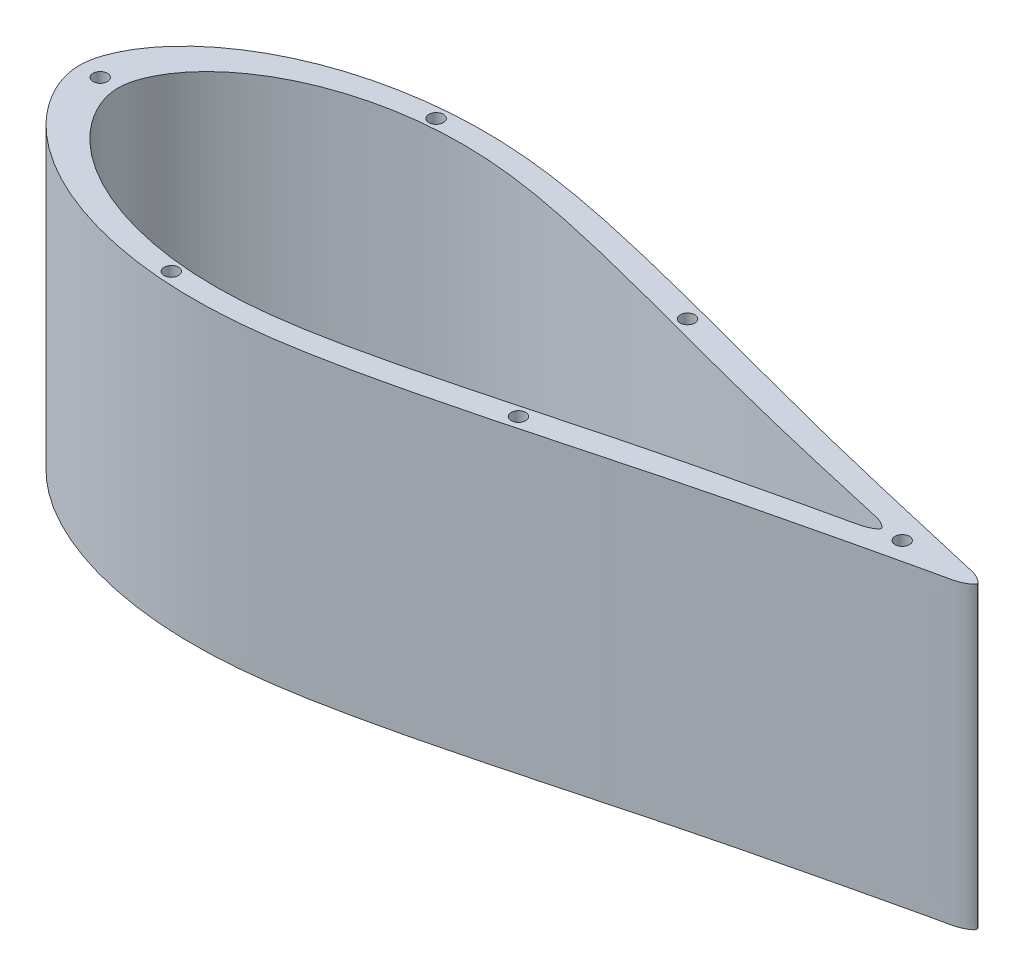
SolidWorks part; units mm, degrees
material "6061 Alloy"
ref_plane "Front Plane" through (0, 0, 0) normal (0, 0, 1) x (1, 0, 0)
ref_plane "Top Plane" through (0, 0, 0) normal (0, 1, 0) x (1, 0, 0)
ref_plane "Right Plane" through (0, 0, 0) normal (1, 0, 0) x (0, 0, -1)
curve "Curve2"
  spline degree 3 poles (0.6483, 0, -5.7987) (-0.3085, 0, 0) (0.6483, 0, 5.7987) (3.0311, 0, 11.5336) (6.6533, 0, 17.267) (11.4717, 0, 22.8371) (17.4302, 0, 28.1154) (24.4659, 0, 32.9986) (32.5279, 0, 37.3723) (41.5389, 0, 41.1607) (51.4314, 0, 44.2651) (62.1158, 0, 46.6282) (73.526, 0, 48.1549) (85.6114, 0, 48.7284) (98.3426, 0, 48.3105) (111.7257, 0, 46.8479) (125.7606, 0, 44.4122) (140.4343, 0, 41.2887) (155.6347, 0, 37.6615) (171.177, 0, 33.6995) (186.8539, 0, 29.5664) (202.4318, 0, 25.4194) (217.9957, 0, 21.2663) (233.2084, 0, 17.405) (247.6838, 0, 13.8748) (260.7251, 0, 10.7897) (272.1052, 0, 8.143) (281.7116, 0, 5.9794) (289.2075, 0, 4.169) (295.0367, 0, 3.0969) (298.1709, 0, 1.895) (300.5776, 0, 0) (298.1709, 0, -1.895) (295.0367, 0, -3.0969) (289.2075, 0, -4.169) (281.7116, 0, -5.9794) (272.1052, 0, -8.143) (260.7251, 0, -10.7897) (247.6838, 0, -13.8748) (233.2084, 0, -17.405) (217.9957, 0, -21.2663) (202.4318, 0, -25.4194) (186.8539, 0, -29.5664) (171.177, 0, -33.6995) (155.6347, 0, -37.6615) (140.4343, 0, -41.2887) (125.7606, 0, -44.4122) (111.7257, 0, -46.8479) (98.3426, 0, -48.3105) (85.6114, 0, -48.7284) (73.526, 0, -48.1549) (62.1158, 0, -46.6282) (51.4314, 0, -44.2651) (41.5389, 0, -41.1607) (32.5279, 0, -37.3723) (24.4659, 0, -32.9986) (17.4302, 0, -28.1154) (11.4717, 0, -22.8371) (6.6533, 0, -17.267) (3.0311, 0, -11.5336) (0.6483, 0, -5.7987) (-0.3085, 0, 0) (0.6483, 0, 5.7987) knots -0.028335 -0.018012 -0.008569 0 0.008569 0.018012 0.028335 0.039554 0.051691 0.064762 0.078763 0.093696 0.109541 0.126268 0.143841 0.162293 0.181715 0.202223 0.224008 0.247042 0.271046 0.295702 0.320629 0.34543 0.369662 0.394535 0.417436 0.438027 0.456004 0.47109 0.483065 0.49175 0.497395 0.5 0.502605 0.50825 0.516935 0.52891 0.543996 0.561973 0.582564 0.605465 0.630338 0.65457 0.679371 0.704298 0.728954 0.752958 0.775992 0.797777 0.818285 0.837707 0.856159 0.873732 0.890459 0.906304 0.921237 0.935238 0.948309 0.960446 0.971665 0.981988 0.991431 1 1.008569 1.018012 1.028335 periodic
sketch "Sketch3" plane through (0, 0, 0) normal (0, 1, 0) x (1, 0, 0)
  spline S0 degree 3 poles (0.6483, 5.7987) (-0.3085, 0) (0.6483, -5.7987) (3.0311, -11.5336) (6.6533, -17.267) (11.4717, -22.8371) (17.4302, -28.1154) (24.4659, -32.9986) (32.5279, -37.3723) (41.5389, -41.1607) (51.4314, -44.2651) (62.1158, -46.6282) (73.526, -48.1549) (85.6114, -48.7284) (98.3426, -48.3105) (111.7257, -46.8479) (125.7606, -44.4122) (140.4343, -41.2887) (155.6347, -37.6615) (171.177, -33.6995) (186.8539, -29.5664) (202.4318, -25.4194) (217.9957, -21.2663) (233.2084, -17.405) (247.6838, -13.8748) (260.7251, -10.7897) (272.1052, -8.143) (281.7116, -5.9794) (289.2075, -4.169) (295.0367, -3.0969) (298.1709, -1.895) (300.5776, 0) (298.1709, 1.895) (295.0367, 3.0969) (289.2075, 4.169) (281.7116, 5.9794) (272.1052, 8.143) (260.7251, 10.7897) (247.6838, 13.8748) (233.2084, 17.405) (217.9957, 21.2663) (202.4318, 25.4194) (186.8539, 29.5664) (171.177, 33.6995) (155.6347, 37.6615) (140.4343, 41.2887) (125.7606, 44.4122) (111.7257, 46.8479) (98.3426, 48.3105) (85.6114, 48.7284) (73.526, 48.1549) (62.1158, 46.6282) (51.4314, 44.2651) (41.5389, 41.1607) (32.5279, 37.3723) (24.4659, 32.9986) (17.4302, 28.1154) (11.4717, 22.8371) (6.6533, 17.267) (3.0311, 11.5336) (0.6483, 5.7987) (-0.3085, 0) (0.6483, -5.7987) knots -0.028335 -0.018012 -0.008569 0 0.008569 0.018012 0.028335 0.039554 0.051691 0.064762 0.078763 0.093696 0.109541 0.126268 0.143841 0.162293 0.181715 0.202223 0.224008 0.247042 0.271046 0.295702 0.320629 0.34543 0.369662 0.394535 0.417436 0.438027 0.456004 0.47109 0.483065 0.49175 0.497395 0.5 0.502605 0.50825 0.516935 0.52891 0.543996 0.561973 0.582564 0.605465 0.630338 0.65457 0.679371 0.704298 0.728954 0.752958 0.775992 0.797777 0.818285 0.837707 0.856159 0.873732 0.890459 0.906304 0.921237 0.935238 0.948309 0.960446 0.971665 0.981988 0.991431 1 1.008569 1.018012 1.028335 only from (0, 0) to (0, 0) construction
  spline S1 degree 3 poles (0.6483, 5.7987) (-0.3085, 0) (0.6483, -5.7987) (3.0311, -11.5336) (6.6533, -17.267) (11.4717, -22.8371) (17.4302, -28.1154) (24.4659, -32.9986) (32.5279, -37.3723) (41.5389, -41.1607) (51.4314, -44.2651) (62.1158, -46.6282) (73.526, -48.1549) (85.6114, -48.7284) (98.3426, -48.3105) (111.7257, -46.8479) (125.7606, -44.4122) (140.4343, -41.2887) (155.6347, -37.6615) (171.177, -33.6995) (186.8539, -29.5664) (202.4318, -25.4194) (217.9957, -21.2663) (233.2084, -17.405) (247.6838, -13.8748) (260.7251, -10.7897) (272.1052, -8.143) (281.7116, -5.9794) (289.2075, -4.169) (295.0367, -3.0969) (298.1709, -1.895) (300.5776, 0) (298.1709, 1.895) (295.0367, 3.0969) (289.2075, 4.169) (281.7116, 5.9794) (272.1052, 8.143) (260.7251, 10.7897) (247.6838, 13.8748) (233.2084, 17.405) (217.9957, 21.2663) (202.4318, 25.4194) (186.8539, 29.5664) (171.177, 33.6995) (155.6347, 37.6615) (140.4343, 41.2887) (125.7606, 44.4122) (111.7257, 46.8479) (98.3426, 48.3105) (85.6114, 48.7284) (73.526, 48.1549) (62.1158, 46.6282) (51.4314, 44.2651) (41.5389, 41.1607) (32.5279, 37.3723) (24.4659, 32.9986) (17.4302, 28.1154) (11.4717, 22.8371) (6.6533, 17.267) (3.0311, 11.5336) (0.6483, 5.7987) (-0.3085, 0) (0.6483, -5.7987) knots -0.028335 -0.018012 -0.008569 0 0.008569 0.018012 0.028335 0.039554 0.051691 0.064762 0.078763 0.093696 0.109541 0.126268 0.143841 0.162293 0.181715 0.202223 0.224008 0.247042 0.271046 0.295702 0.320629 0.34543 0.369662 0.394535 0.417436 0.438027 0.456004 0.47109 0.483065 0.49175 0.497395 0.5 0.502605 0.50825 0.516935 0.52891 0.543996 0.561973 0.582564 0.605465 0.630338 0.65457 0.679371 0.704298 0.728954 0.752958 0.775992 0.797777 0.818285 0.837707 0.856159 0.873732 0.890459 0.906304 0.921237 0.935238 0.948309 0.960446 0.971665 0.981988 0.991431 1 1.008569 1.018012 1.028335 only from (0, 0) to (0, 0)
extrude "Boss-Extrude1" add sketch "Sketch3" along normal blind 100
sketch "Sketch4" plane through (0, 0, 0) normal (0, -1, 0) x (1, 0, 0)
  spline S1 degree 3 poles (299.9957, 0.014) (299.9938, -0.0895) (299.9638, -0.2086) (299.9031, -0.3373) (299.8291, -0.4596) (299.7174, -0.5996) (299.5918, -0.7263) (299.4861, -0.8218) (299.4046, -0.8909) (299.3213, -0.9578) (299.2087, -1.0447) (299.0654, -1.1499) (298.8903, -1.2715) (298.7126, -1.3891) (298.3525, -1.6168) (297.92, -1.8622) (297.411, -2.1134) (297.0223, -2.287) (296.6272, -2.4451) (296.2267, -2.5893) (295.822, -2.722) (295.4141, -2.8452) (295.0041, -2.961) (294.5925, -3.0704) (294.0419, -3.2092) (293.4889, -3.3386) (292.9344, -3.4614) (292.5179, -3.5509) (292.101, -3.6386) (291.5448, -3.754) (290.9884, -3.8677) (290.4319, -3.9815) (289.8757, -4.0959) (289.1809, -4.2414) (288.3483, -4.4216) (286.6852, -4.7905) (284.1958, -5.3676) (281.4314, -6.0157) (279.2189, -6.5298) (277.0055, -7.0405) (274.7915, -7.5479) (272.5773, -8.0547) (270.9166, -8.4349) (269.2562, -8.816) (267.0427, -9.3258) (264.2767, -9.9669) (259.8527, -10.9999) (254.3255, -12.3029) (248.8019, -13.6215) (244.3858, -14.6874) (239.9714, -15.7609) (234.4573, -17.1179) (228.9488, -18.4974) (224.5457, -19.6156) (217.945, -21.3082) (208.0596, -23.9078) (194.8919, -27.424) (183.9159, -30.3428) (175.1284, -32.6526) (166.3345, -34.9377) (158.628, -36.8918) (152.0088, -38.511) (148.6961, -39.3081) (145.3801, -40.0913) (142.0605, -40.8591) (138.737, -41.6097) (135.4091, -42.3409) (132.0764, -43.0503) (127.626, -43.9641) (122.0492, -45.0405) (113.0926, -46.5738) (104.0773, -47.7374) (95.0123, -48.3913) (88.1991, -48.6052) (81.3834, -48.5233) (74.5794, -48.1282) (67.8019, -47.4032) (61.0693, -46.3378) (54.4011, -44.9234) (47.8168, -43.1503) (41.3469, -40.998) (35.028, -38.4414) (28.8957, -35.456) (23.013, -32.0075) (18.3744, -28.7213) (14.8691, -25.8285) (12.3582, -23.5227) (9.984, -21.0765) (8.1373, -18.9185) (6.7509, -17.1189) (5.7603, -15.7327) (4.8235, -14.3098) (3.9449, -12.8503) (3.2654, -11.6036) (2.7565, -10.5882) (2.0291, -9.0471) (1.0809, -6.6677) (0.2183, -3.3645) (-0.1054, 0.0396) (0.2336, 3.4379) (0.961, 6.1924) (1.7397, 8.3272) (2.4132, 9.8934) (3.1645, 11.4234) (3.9845, 12.9173) (4.8661, 14.375) (6.1184, 16.2702) (8.4977, 19.4595) (11.5773, 22.8096) (14.9283, 25.8792) (17.5601, 28.0457) (20.2943, 30.0805) (22.6482, 31.6695) (24.5714, 32.8789) (26.5195, 34.0477) (29.9892, 35.9887) (35.0983, 38.4733) (41.419, 41.0252) (46.8122, 42.8146) (51.1842, 44.0565) (55.5891, 45.1756) (63.3708, 46.8228) (74.6452, 48.3036) (88.2816, 48.7503) (101.9024, 48.0274) (113.1705, 46.5598) (122.1264, 45.0264) (128.8176, 43.735) (135.487, 42.3362) (142.1376, 40.8488) (148.7724, 39.2926) (157.6025, 37.1514) (173.0143, 33.2397) (190.5764, 28.5711) (208.1372, 23.899) (221.3117, 20.4089) (234.5313, 17.0929) (245.5623, 14.3906) (254.4011, 12.2854) (261.0337, 10.722) (266.5649, 9.436) (270.9921, 8.4173) (274.3131, 7.6559) (277.6343, 6.8948) (280.9537, 6.1266) (284.2713, 5.3501) (287.59, 4.5785) (290.368, 3.9915) (292.5952, 3.5417) (294.2576, 3.1677) (295.6314, 2.798) (296.7027, 2.4227) (297.4846, 2.0873) (298.1125, 1.7565) (298.5991, 1.4632) (298.8968, 1.2692) (299.1297, 1.1058) (299.3003, 0.9778) (299.438, 0.8649) (299.5442, 0.7698) (299.6215, 0.6957) (299.6958, 0.6184) (299.7894, 0.5104) (299.8729, 0.3935) (299.9377, 0.2672) (299.9677, 0.1847) (299.984, 0.117) (299.9921, 0.0657) (299.9957, 0.014) (299.9938, -0.0895) (299.9638, -0.2086) knots -0.000244 -0.000163 -0.000081 0 0.000326 0.000488 0.000651 0.000977 0.001302 0.001465 0.001628 0.00179 0.001953 0.002279 0.002604 0.00293 0.003255 0.004557 0.005208 0.005859 0.00651 0.007161 0.007812 0.008464 0.009115 0.009766 0.010417 0.011719 0.01237 0.013021 0.013672 0.014323 0.015625 0.016276 0.016927 0.018229 0.019531 0.020833 0.026042 0.03125 0.033854 0.036458 0.041667 0.044271 0.046875 0.049479 0.052083 0.057292 0.0625 0.072917 0.083333 0.088542 0.09375 0.104167 0.114583 0.119792 0.125 0.145833 0.166667 0.1875 0.197917 0.208333 0.229167 0.234375 0.239583 0.244792 0.25 0.255208 0.260417 0.265625 0.270833 0.28125 0.291667 0.3125 0.322917 0.333333 0.34375 0.354167 0.364583 0.375 0.385417 0.395833 0.40625 0.416667 0.427083 0.4375 0.447917 0.453125 0.458333 0.463542 0.46875 0.471354 0.473958 0.476562 0.479167 0.481771 0.483073 0.484375 0.489583 0.494792 0.5 0.505208 0.510417 0.513021 0.515625 0.518229 0.520833 0.523438 0.526042 0.53125 0.541667 0.546875 0.552083 0.557292 0.5625 0.565104 0.567708 0.572917 0.583333 0.59375 0.604167 0.609375 0.614583 0.625 0.645833 0.666667 0.6875 0.708333 0.71875 0.729167 0.739583 0.75 0.760417 0.770833 0.791667 0.833333 0.854167 0.875 0.895833 0.916667 0.927083 0.9375 0.947917 0.953125 0.958333 0.963542 0.96875 0.973958 0.979167 0.984375 0.986979 0.989583 0.992188 0.99349 0.994792 0.996094 0.996745 0.997396 0.997721 0.998047 0.998372 0.998535 0.998698 0.998861 0.999023 0.999349 0.999512 0.999674 0.999756 0.999837 0.999919 1 1.000326 1.000488 1.000651 only from (299.9939, -0.0377) to (299.9939, -0.0377)
  spline S3 degree 3 poles (299.9957, 0.014) (299.9938, -0.0895) (299.9638, -0.2086) (299.9031, -0.3373) (299.8291, -0.4596) (299.7174, -0.5996) (299.5918, -0.7263) (299.4861, -0.8218) (299.4046, -0.8909) (299.3213, -0.9578) (299.2087, -1.0447) (299.0654, -1.1499) (298.8903, -1.2715) (298.7126, -1.3891) (298.3525, -1.6168) (297.92, -1.8622) (297.411, -2.1134) (297.0223, -2.287) (296.6272, -2.4451) (296.2267, -2.5893) (295.822, -2.722) (295.4141, -2.8452) (295.0041, -2.961) (294.5925, -3.0704) (294.0419, -3.2092) (293.4889, -3.3386) (292.9344, -3.4614) (292.5179, -3.5509) (292.101, -3.6386) (291.5448, -3.754) (290.9884, -3.8677) (290.4319, -3.9815) (289.8757, -4.0959) (289.1809, -4.2414) (288.3483, -4.4216) (286.6852, -4.7905) (284.1958, -5.3676) (281.4314, -6.0157) (279.2189, -6.5298) (277.0055, -7.0405) (274.7915, -7.5479) (272.5773, -8.0547) (270.9166, -8.4349) (269.2562, -8.816) (267.0427, -9.3258) (264.2767, -9.9669) (259.8527, -10.9999) (254.3255, -12.3029) (248.8019, -13.6215) (244.3858, -14.6874) (239.9714, -15.7609) (234.4573, -17.1179) (228.9488, -18.4974) (224.5457, -19.6156) (217.945, -21.3082) (208.0596, -23.9078) (194.8919, -27.424) (183.9159, -30.3428) (175.1284, -32.6526) (166.3345, -34.9377) (158.628, -36.8918) (152.0088, -38.511) (148.6961, -39.3081) (145.3801, -40.0913) (142.0605, -40.8591) (138.737, -41.6097) (135.4091, -42.3409) (132.0764, -43.0503) (127.626, -43.9641) (122.0492, -45.0405) (113.0926, -46.5738) (104.0773, -47.7374) (95.0123, -48.3913) (88.1991, -48.6052) (81.3834, -48.5233) (74.5794, -48.1282) (67.8019, -47.4032) (61.0693, -46.3378) (54.4011, -44.9234) (47.8168, -43.1503) (41.3469, -40.998) (35.028, -38.4414) (28.8957, -35.456) (23.013, -32.0075) (18.3744, -28.7213) (14.8691, -25.8285) (12.3582, -23.5227) (9.984, -21.0765) (8.1373, -18.9185) (6.7509, -17.1189) (5.7603, -15.7327) (4.8235, -14.3098) (3.9449, -12.8503) (3.2654, -11.6036) (2.7565, -10.5882) (2.0291, -9.0471) (1.0809, -6.6677) (0.2183, -3.3645) (-0.1054, 0.0396) (0.2336, 3.4379) (0.961, 6.1924) (1.7397, 8.3272) (2.4132, 9.8934) (3.1645, 11.4234) (3.9845, 12.9173) (4.8661, 14.375) (6.1184, 16.2702) (8.4977, 19.4595) (11.5773, 22.8096) (14.9283, 25.8792) (17.5601, 28.0457) (20.2943, 30.0805) (22.6482, 31.6695) (24.5714, 32.8789) (26.5195, 34.0477) (29.9892, 35.9887) (35.0983, 38.4733) (41.419, 41.0252) (46.8122, 42.8146) (51.1842, 44.0565) (55.5891, 45.1756) (63.3708, 46.8228) (74.6452, 48.3036) (88.2816, 48.7503) (101.9024, 48.0274) (113.1705, 46.5598) (122.1264, 45.0264) (128.8176, 43.735) (135.487, 42.3362) (142.1376, 40.8488) (148.7724, 39.2926) (157.6025, 37.1514) (173.0143, 33.2397) (190.5764, 28.5711) (208.1372, 23.899) (221.3117, 20.4089) (234.5313, 17.0929) (245.5623, 14.3906) (254.4011, 12.2854) (261.0337, 10.722) (266.5649, 9.436) (270.9921, 8.4173) (274.3131, 7.6559) (277.6343, 6.8948) (280.9537, 6.1266) (284.2713, 5.3501) (287.59, 4.5785) (290.368, 3.9915) (292.5952, 3.5417) (294.2576, 3.1677) (295.6314, 2.798) (296.7027, 2.4227) (297.4846, 2.0873) (298.1125, 1.7565) (298.5991, 1.4632) (298.8968, 1.2692) (299.1297, 1.1058) (299.3003, 0.9778) (299.438, 0.8649) (299.5442, 0.7698) (299.6215, 0.6957) (299.6958, 0.6184) (299.7894, 0.5104) (299.8729, 0.3935) (299.9377, 0.2672) (299.9677, 0.1847) (299.984, 0.117) (299.9921, 0.0657) (299.9957, 0.014) (299.9938, -0.0895) (299.9638, -0.2086) knots -0.000244 -0.000163 -0.000081 0 0.000326 0.000488 0.000651 0.000977 0.001302 0.001465 0.001628 0.00179 0.001953 0.002279 0.002604 0.00293 0.003255 0.004557 0.005208 0.005859 0.00651 0.007161 0.007812 0.008464 0.009115 0.009766 0.010417 0.011719 0.01237 0.013021 0.013672 0.014323 0.015625 0.016276 0.016927 0.018229 0.019531 0.020833 0.026042 0.03125 0.033854 0.036458 0.041667 0.044271 0.046875 0.049479 0.052083 0.057292 0.0625 0.072917 0.083333 0.088542 0.09375 0.104167 0.114583 0.119792 0.125 0.145833 0.166667 0.1875 0.197917 0.208333 0.229167 0.234375 0.239583 0.244792 0.25 0.255208 0.260417 0.265625 0.270833 0.28125 0.291667 0.3125 0.322917 0.333333 0.34375 0.354167 0.364583 0.375 0.385417 0.395833 0.40625 0.416667 0.427083 0.4375 0.447917 0.453125 0.458333 0.463542 0.46875 0.471354 0.473958 0.476562 0.479167 0.481771 0.483073 0.484375 0.489583 0.494792 0.5 0.505208 0.510417 0.513021 0.515625 0.518229 0.520833 0.523438 0.526042 0.53125 0.541667 0.546875 0.552083 0.557292 0.5625 0.565104 0.567708 0.572917 0.583333 0.59375 0.604167 0.609375 0.614583 0.625 0.645833 0.666667 0.6875 0.708333 0.71875 0.729167 0.739583 0.75 0.760417 0.770833 0.791667 0.833333 0.854167 0.875 0.895833 0.916667 0.927083 0.9375 0.947917 0.953125 0.958333 0.963542 0.96875 0.973958 0.979167 0.984375 0.986979 0.989583 0.992188 0.99349 0.994792 0.996094 0.996745 0.997396 0.997721 0.998047 0.998372 0.998535 0.998698 0.998861 0.999023 0.999349 0.999512 0.999674 0.999756 0.999837 0.999919 1 1.000326 1.000488 1.000651 only from (299.9939, -0.0377) to (299.9939, -0.0377)
  point P0 (0, 0)
sketch "Sketch12" plane through (0, 100, 0) normal (0, 1, 0) x (1, 0, 0)
  line L0 (0, 0) -> (300, 0)
  circle A0 centre (7, 0) radius 2.415
  circle A1 centre (275, 0) radius 2.415
  circle A2 centre (175, 28.25) radius 2.415
  circle A3 centre (75, 44.25) radius 2.415
  circle A4 centre (75, -44.25) radius 2.415
  circle A5 centre (175, -28.25) radius 2.415
  spline S0 degree 3 poles (0, 0) (0.0127, 0.8519) (0.0873, 2.1289) (0.3851, 3.8086) (0.6701, 5.0543) (1.0208, 6.2831) (1.4295, 7.4936) (1.8916, 8.6847) (2.5723, 10.2466) (3.3403, 11.7685) (4.1821, 13.2499) (4.8481, 14.3404) (5.5463, 15.4104) (6.5173, 16.8095) (8.3173, 19.1857) (11.1491, 22.3759) (14.254, 25.2986) (16.8696, 27.4832) (18.8904, 29.0471) (20.9656, 30.5381) (23.0907, 31.9578) (25.2609, 33.3081) (28.2091, 35.0179) (31.9867, 36.9901) (35.864, 38.7536) (40.2978, 40.5697) (43.6075, 41.7562) (47.2597, 42.9228) (49.1997, 43.4984) (51.5612, 44.1482) (53.6234, 44.6807) (56.9396, 45.4648) (61.1126, 46.32) (66.1561, 47.1501) (72.9181, 48.0008) (81.4191, 48.5904) (91.6468, 48.593) (101.8545, 47.9504) (112.0056, 46.7354) (122.0921, 45.0639) (132.1215, 43.0754) (142.1039, 40.8759) (150.3928, 38.912) (157.0105, 37.2863) (161.968, 36.0435) (166.9206, 34.7813) (171.869, 33.5031) (176.8142, 32.2122) (181.7567, 30.9112) (186.6972, 29.6027) (193.2828, 27.8512) (204.8052, 24.777) (217.9781, 21.2804) (231.1875, 17.9255) (241.1104, 15.4724) (251.047, 13.0749) (259.3371, 11.1171) (265.9742, 9.5723) (270.9544, 8.4242) (275.1062, 7.4744) (278.4271, 6.7123) (280.9168, 6.1366) (283.4056, 5.5565) (285.4789, 5.0702) (287.1394, 4.6894) (288.1786, 4.4576) (289.2192, 4.2324) (290.0528, 4.0579) (290.8872, 3.8865) (291.5132, 3.7583) (292.139, 3.6296) (292.7643, 3.4981) (293.5966, 3.316) (294.6334, 3.07) (295.866, 2.7259) (296.8663, 2.362) (297.6392, 2.006) (298.2033, 1.7065) (298.7487, 1.3731) (299.1892, 1.0705) (299.4789, 0.8336) (299.6341, 0.6863) (299.7434, 0.5687) (299.8419, 0.4423) (299.9099, 0.3285) (299.9514, 0.232) (299.975, 0.157) (299.9877, 0.0922) (299.9951, 0.0396) (299.9984, 0.0132) (300, 0) knots 0 0 0 0 0.007812 0.011719 0.015625 0.019531 0.023438 0.027344 0.03125 0.039062 0.042969 0.046875 0.050781 0.054688 0.0625 0.078125 0.09375 0.101562 0.109375 0.117188 0.125 0.132812 0.140625 0.15625 0.171875 0.179688 0.200195 0.204102 0.214844 0.21875 0.226562 0.234375 0.25 0.265625 0.28125 0.3125 0.34375 0.375 0.40625 0.4375 0.46875 0.5 0.53125 0.546875 0.5625 0.578125 0.59375 0.609375 0.625 0.640625 0.65625 0.6875 0.75 0.78125 0.8125 0.84375 0.875 0.890625 0.90625 0.921875 0.929688 0.9375 0.945312 0.953125 0.957031 0.960938 0.962891 0.966797 0.96875 0.970703 0.972656 0.974609 0.976562 0.980469 0.984375 0.988281 0.990234 0.992188 0.994141 0.996094 0.99707 0.997559 0.998047 0.998535 0.999023 0.999268 0.999512 0.999756 0.999878 1 1 1 1
  spline S1 degree 3 poles (300, 0) (299.9969, -0.0265) (299.9902, -0.0793) (299.9697, -0.1828) (299.9329, -0.2812) (299.8829, -0.374) (299.8257, -0.4633) (299.7598, -0.5476) (299.6885, -0.6275) (299.6328, -0.6854) (299.5754, -0.7415) (299.497, -0.8142) (299.3958, -0.9014) (299.2287, -1.0344) (299.0124, -1.1909) (298.7909, -1.3395) (298.6114, -1.4544) (298.4302, -1.5666) (297.9255, -1.8637) (297.0661, -2.2889) (295.4641, -2.8701) (293.8044, -3.2738) (292.3482, -3.59) (291.514, -3.7623) (290.888, -3.89) (290.262, -4.0174) (289.6363, -4.1465) (289.1154, -4.2561) (288.6989, -4.3453) (288.0746, -4.4805) (287.1392, -4.6884) (285.8937, -4.9736) (284.6493, -5.2635) (282.9906, -5.6522) (280.9169, -6.1368) (277.5971, -6.9039) (274.2756, -7.6635) (270.1244, -8.6154) (266.8044, -9.3814) (263.4857, -10.1531) (258.509, -11.316) (251.0484, -13.0802) (237.7992, -16.2753) (224.5768, -19.5795) (211.3916, -23.0284) (201.5132, -25.6558) (193.283, -27.8519) (186.6974, -29.6034) (181.7568, -30.9116) (176.8141, -32.2119) (170.2204, -33.9319) (163.6199, -35.626) (157.0098, -37.2817) (152.0466, -38.5015) (147.0766, -39.693) (142.9283, -40.6582) (139.6054, -41.4112) (137.5265, -41.8731) (135.8622, -42.2368) (134.197, -42.5965) (132.1138, -43.0383) (129.6112, -43.5558) (126.2702, -44.2266) (117.0658, -45.9837) (105.2582, -47.7371) (91.6466, -48.5923) (81.4194, -48.5903) (71.2173, -47.8821) (62.7809, -46.6624) (56.1041, -45.2948) (51.1408, -44.0685) (46.2329, -42.6347) (41.3932, -40.9845) (37.4311, -39.4197) (34.3123, -38.0485) (31.2304, -36.5957) (27.4526, -34.6233) (23.7976, -32.4309) (20.9639, -30.5381) (18.8886, -29.0472) (16.8678, -27.4834) (14.2522, -25.2987) (11.7687, -22.9607) (9.4503, -20.4625) (8.0782, -18.8333) (7.1625, -17.6569) (6.2706, -16.4624) (5.2981, -15.0631) (4.2869, -13.435) (3.5509, -12.1389) (2.9565, -11.0075) (2.217, -9.4721) (1.4015, -7.5028) (0.6443, -5.0621) (0.1175, -2.5546) (0.0114, -0.8519) (0, 0) knots 0 0 0 0 0.000244 0.000488 0.000977 0.001221 0.001465 0.001953 0.002197 0.002441 0.002686 0.00293 0.003418 0.003906 0.004883 0.005859 0.006348 0.006836 0.007812 0.011719 0.015625 0.023438 0.027344 0.029297 0.03125 0.033203 0.035156 0.037109 0.038086 0.039062 0.042969 0.046875 0.050781 0.054688 0.0625 0.070312 0.085938 0.09375 0.109375 0.117188 0.125 0.15625 0.1875 0.25 0.28125 0.3125 0.34375 0.359375 0.375 0.390625 0.40625 0.4375 0.453125 0.46875 0.484375 0.5 0.507812 0.515625 0.519531 0.523438 0.53125 0.539062 0.546875 0.5625 0.625 0.65625 0.6875 0.71875 0.75 0.765625 0.78125 0.796875 0.8125 0.828125 0.835938 0.84375 0.859375 0.875 0.882812 0.890625 0.898438 0.90625 0.921875 0.929688 0.9375 0.941406 0.943359 0.951172 0.957031 0.960938 0.964844 0.96875 0.976562 0.984375 0.992188 1 1 1 1
  spline S2 degree 3 poles (0, 0) (0.0127, 0.8519) (0.0873, 2.1289) (0.3851, 3.8086) (0.6701, 5.0543) (1.0208, 6.2831) (1.4295, 7.4936) (1.8916, 8.6847) (2.5723, 10.2466) (3.3403, 11.7685) (4.1821, 13.2499) (4.8481, 14.3404) (5.5463, 15.4104) (6.5173, 16.8095) (8.3173, 19.1857) (11.1491, 22.3759) (14.254, 25.2986) (16.8696, 27.4832) (18.8904, 29.0471) (20.9656, 30.5381) (23.0907, 31.9578) (25.2609, 33.3081) (28.2091, 35.0179) (31.9867, 36.9901) (35.864, 38.7536) (40.2978, 40.5697) (43.6075, 41.7562) (47.2597, 42.9228) (49.1997, 43.4984) (51.5612, 44.1482) (53.6234, 44.6807) (56.9396, 45.4648) (61.1126, 46.32) (66.1561, 47.1501) (72.9181, 48.0008) (81.4191, 48.5904) (91.6468, 48.593) (101.8545, 47.9504) (112.0056, 46.7354) (122.0921, 45.0639) (132.1215, 43.0754) (142.1039, 40.8759) (150.3928, 38.912) (157.0105, 37.2863) (161.968, 36.0435) (166.9206, 34.7813) (171.869, 33.5031) (176.8142, 32.2122) (181.7567, 30.9112) (186.6972, 29.6027) (193.2828, 27.8512) (204.8052, 24.777) (217.9781, 21.2804) (231.1875, 17.9255) (241.1104, 15.4724) (251.047, 13.0749) (259.3371, 11.1171) (265.9742, 9.5723) (270.9544, 8.4242) (275.1062, 7.4744) (278.4271, 6.7123) (280.9168, 6.1366) (283.4056, 5.5565) (285.4789, 5.0702) (287.1394, 4.6894) (288.1786, 4.4576) (289.2192, 4.2324) (290.0528, 4.0579) (290.8872, 3.8865) (291.5132, 3.7583) (292.139, 3.6296) (292.7643, 3.4981) (293.5966, 3.316) (294.6334, 3.07) (295.866, 2.7259) (296.8663, 2.362) (297.6392, 2.006) (298.2033, 1.7065) (298.7487, 1.3731) (299.1892, 1.0705) (299.4789, 0.8336) (299.6341, 0.6863) (299.7434, 0.5687) (299.8419, 0.4423) (299.9099, 0.3285) (299.9514, 0.232) (299.975, 0.157) (299.9877, 0.0922) (299.9951, 0.0396) (299.9984, 0.0132) (300, 0) knots 0 0 0 0 0.007812 0.011719 0.015625 0.019531 0.023438 0.027344 0.03125 0.039062 0.042969 0.046875 0.050781 0.054688 0.0625 0.078125 0.09375 0.101562 0.109375 0.117188 0.125 0.132812 0.140625 0.15625 0.171875 0.179688 0.200195 0.204102 0.214844 0.21875 0.226562 0.234375 0.25 0.265625 0.28125 0.3125 0.34375 0.375 0.40625 0.4375 0.46875 0.5 0.53125 0.546875 0.5625 0.578125 0.59375 0.609375 0.625 0.640625 0.65625 0.6875 0.75 0.78125 0.8125 0.84375 0.875 0.890625 0.90625 0.921875 0.929688 0.9375 0.945312 0.953125 0.957031 0.960938 0.962891 0.966797 0.96875 0.970703 0.972656 0.974609 0.976562 0.980469 0.984375 0.988281 0.990234 0.992188 0.994141 0.996094 0.99707 0.997559 0.998047 0.998535 0.999023 0.999268 0.999512 0.999756 0.999878 1 1 1 1
  spline S3 degree 3 poles (300, 0) (299.9969, -0.0265) (299.9902, -0.0793) (299.9697, -0.1828) (299.9329, -0.2812) (299.8829, -0.374) (299.8257, -0.4633) (299.7598, -0.5476) (299.6885, -0.6275) (299.6328, -0.6854) (299.5754, -0.7415) (299.497, -0.8142) (299.3958, -0.9014) (299.2287, -1.0344) (299.0124, -1.1909) (298.7909, -1.3395) (298.6114, -1.4544) (298.4302, -1.5666) (297.9255, -1.8637) (297.0661, -2.2889) (295.4641, -2.8701) (293.8044, -3.2738) (292.3482, -3.59) (291.514, -3.7623) (290.888, -3.89) (290.262, -4.0174) (289.6363, -4.1465) (289.1154, -4.2561) (288.6989, -4.3453) (288.0746, -4.4805) (287.1392, -4.6884) (285.8937, -4.9736) (284.6493, -5.2635) (282.9906, -5.6522) (280.9169, -6.1368) (277.5971, -6.9039) (274.2756, -7.6635) (270.1244, -8.6154) (266.8044, -9.3814) (263.4857, -10.1531) (258.509, -11.316) (251.0484, -13.0802) (237.7992, -16.2753) (224.5768, -19.5795) (211.3916, -23.0284) (201.5132, -25.6558) (193.283, -27.8519) (186.6974, -29.6034) (181.7568, -30.9116) (176.8141, -32.2119) (170.2204, -33.9319) (163.6199, -35.626) (157.0098, -37.2817) (152.0466, -38.5015) (147.0766, -39.693) (142.9283, -40.6582) (139.6054, -41.4112) (137.5265, -41.8731) (135.8622, -42.2368) (134.197, -42.5965) (132.1138, -43.0383) (129.6112, -43.5558) (126.2702, -44.2266) (117.0658, -45.9837) (105.2582, -47.7371) (91.6466, -48.5923) (81.4194, -48.5903) (71.2173, -47.8821) (62.7809, -46.6624) (56.1041, -45.2948) (51.1408, -44.0685) (46.2329, -42.6347) (41.3932, -40.9845) (37.4311, -39.4197) (34.3123, -38.0485) (31.2304, -36.5957) (27.4526, -34.6233) (23.7976, -32.4309) (20.9639, -30.5381) (18.8886, -29.0472) (16.8678, -27.4834) (14.2522, -25.2987) (11.7687, -22.9607) (9.4503, -20.4625) (8.0782, -18.8333) (7.1625, -17.6569) (6.2706, -16.4624) (5.2981, -15.0631) (4.2869, -13.435) (3.5509, -12.1389) (2.9565, -11.0075) (2.217, -9.4721) (1.4015, -7.5028) (0.6443, -5.0621) (0.1175, -2.5546) (0.0114, -0.8519) (0, 0) knots 0 0 0 0 0.000244 0.000488 0.000977 0.001221 0.001465 0.001953 0.002197 0.002441 0.002686 0.00293 0.003418 0.003906 0.004883 0.005859 0.006348 0.006836 0.007812 0.011719 0.015625 0.023438 0.027344 0.029297 0.03125 0.033203 0.035156 0.037109 0.038086 0.039062 0.042969 0.046875 0.050781 0.054688 0.0625 0.070312 0.085938 0.09375 0.109375 0.117188 0.125 0.15625 0.1875 0.25 0.28125 0.3125 0.34375 0.359375 0.375 0.390625 0.40625 0.4375 0.453125 0.46875 0.484375 0.5 0.507812 0.515625 0.519531 0.523438 0.53125 0.539062 0.546875 0.5625 0.625 0.65625 0.6875 0.71875 0.75 0.765625 0.78125 0.796875 0.8125 0.828125 0.835938 0.84375 0.859375 0.875 0.882812 0.890625 0.898438 0.90625 0.921875 0.929688 0.9375 0.941406 0.943359 0.951172 0.957031 0.960938 0.964844 0.96875 0.976562 0.984375 0.992188 1 1 1 1
  point P16 (0, 0)
  point P17 (0, 0)
  point P18 (0, 0)
  point P19 (0, 0)
  point P20 (0, 0)
  dimension "D1" = 4.83
  dimension "D2" = 44.25
  dimension "D3" = 28.25
  dimension "D4" = 75
  dimension "D5" = 100
  dimension "D6" = 100
  dimension "D7" = 7
extrude "Cut-Extrude8" cut sketch "Sketch12" against normal up to surface (100 mm away) contours L0 A1 | L0 A1 | A3 | L0 A0 | L0 A0 | A4 | A5 | A2
sketch "Sketch13" plane through (0, 100, 0) normal (0, 1, 0) x (1, 0, 0)
  line L0 (0, 0) -> (300, 0) construction
  spline S0 degree 3 poles (0.6483, 5.7987) (-0.3085, 0) (0.6483, -5.7987) (3.0311, -11.5336) (6.6533, -17.267) (11.4717, -22.8371) (17.4302, -28.1154) (24.4659, -32.9986) (32.5279, -37.3723) (41.5389, -41.1607) (51.4314, -44.2651) (62.1158, -46.6282) (73.526, -48.1549) (85.6114, -48.7284) (98.3426, -48.3105) (111.7257, -46.8479) (125.7606, -44.4122) (140.4343, -41.2887) (155.6347, -37.6615) (171.177, -33.6995) (186.8539, -29.5664) (202.4318, -25.4194) (217.9957, -21.2663) (233.2084, -17.405) (247.6838, -13.8748) (260.7251, -10.7897) (272.1052, -8.143) (281.7116, -5.9794) (289.2075, -4.169) (295.0367, -3.0969) (298.1709, -1.895) (300.5776, 0) (298.1709, 1.895) (295.0367, 3.0969) (289.2075, 4.169) (281.7116, 5.9794) (272.1052, 8.143) (260.7251, 10.7897) (247.6838, 13.8748) (233.2084, 17.405) (217.9957, 21.2663) (202.4318, 25.4194) (186.8539, 29.5664) (171.177, 33.6995) (155.6347, 37.6615) (140.4343, 41.2887) (125.7606, 44.4122) (111.7257, 46.8479) (98.3426, 48.3105) (85.6114, 48.7284) (73.526, 48.1549) (62.1158, 46.6282) (51.4314, 44.2651) (41.5389, 41.1607) (32.5279, 37.3723) (24.4659, 32.9986) (17.4302, 28.1154) (11.4717, 22.8371) (6.6533, 17.267) (3.0311, 11.5336) (0.6483, 5.7987) (-0.3085, 0) (0.6483, -5.7987) knots -0.028335 -0.018012 -0.008569 0 0.008569 0.018012 0.028335 0.039554 0.051691 0.064762 0.078763 0.093696 0.109541 0.126268 0.143841 0.162293 0.181715 0.202223 0.224008 0.247042 0.271046 0.295702 0.320629 0.34543 0.369662 0.394535 0.417436 0.438027 0.456004 0.47109 0.483065 0.49175 0.497395 0.5 0.502605 0.50825 0.516935 0.52891 0.543996 0.561973 0.582564 0.605465 0.630338 0.65457 0.679371 0.704298 0.728954 0.752958 0.775992 0.797777 0.818285 0.837707 0.856159 0.873732 0.890459 0.906304 0.921237 0.935238 0.948309 0.960446 0.971665 0.981988 0.991431 1 1.008569 1.018012 1.028335 only from (0, 0) to (0, 0) construction
  spline S1 degree 3 poles (267.9959, 0.0438) (268.0022, -0.0146) (268.0004, -0.088) (267.9859, -0.1604) (267.9632, -0.2311) (267.9392, -0.2862) (267.9033, -0.3526) (267.8621, -0.4165) (267.788, -0.5133) (267.7053, -0.6026) (267.6175, -0.6863) (267.5497, -0.7467) (267.4802, -0.8051) (267.3382, -0.9181) (267.1173, -1.077) (266.8651, -1.2429) (266.6596, -1.3695) (266.4517, -1.4919) (266.1874, -1.6372) (265.8639, -1.7991) (265.5345, -1.9486) (265.1998, -2.0857) (264.8605, -2.2111) (264.403, -2.3646) (263.8238, -2.5352) (263.1229, -2.7177) (262.4182, -2.8843) (261.475, -3.0908) (259.818, -3.4245) (257.4565, -3.923) (254.636, -4.5802) (251.8159, -5.2396) (248.9944, -5.8927) (246.1714, -6.5396) (243.3485, -7.1868) (240.9965, -7.7278) (239.1154, -8.1628) (236.2942, -8.8173) (233.0042, -9.5871) (228.3067, -10.6971) (223.6116, -11.8175) (217.982, -13.1808) (210.4828, -15.0265) (201.1232, -17.3911) (189.9197, -20.3376) (180.5928, -22.8286) (173.1295, -24.8149) (167.5304, -26.2984) (161.9284, -27.771) (156.3222, -29.2276) (150.7103, -30.6621) (143.2178, -32.5348) (135.707, -34.3339) (128.1694, -36.0176) (122.5001, -37.2061) (116.8116, -38.3048) (109.1988, -39.61) (99.6211, -40.8501) (88.0419, -41.4721) (76.4528, -41.0873) (66.8687, -39.8309) (59.3106, -38.2323) (53.7138, -36.728) (48.2122, -34.9029) (41.0498, -32.011) (34.2011, -28.3896) (27.8874, -23.9267) (24.231, -20.7641) (21.5354, -17.9963) (19.6481, -15.7979) (17.9162, -13.4746) (16.3668, -11.027) (15.0236, -8.4559) (13.9455, -5.7629) (13.2044, -2.9569) (12.9633, -0.5468) (13.0531, 1.3807) (13.3153, 3.2931) (13.9244, 5.6355) (14.9983, 8.3316) (16.3325, 10.9057) (17.8787, 13.3564) (19.3204, 15.2949) (20.5505, 16.7832) (21.5093, 17.8683) (22.5016, 18.9229) (24.5485, 20.9715) (27.1064, 23.188) (29.8145, 25.209) (31.4006, 26.3096) (32.709, 27.1749) (34.1405, 28.0721) (35.5949, 28.9317) (38.4367, 30.5256) (41.6885, 32.1259) (45.4655, 33.7299) (49.0678, 35.1216) (53.6503, 36.6462) (59.2464, 38.1532) (66.8047, 39.7555) (74.4712, 40.7671) (82.1823, 41.214) (87.0097, 41.2711) (90.388, 41.2015) (92.7999, 41.1138) (94.9693, 41.0013) (97.8587, 40.801) (100.263, 40.5877) (102.9035, 40.3112) (105.3004, 40.028) (108.1704, 39.6404) (111.9889, 39.0659) (115.7957, 38.4141) (119.5915, 37.7029) (122.4333, 37.1438) (125.2703, 36.5615) (128.103, 35.9584) (130.9317, 35.3368) (134.6983, 34.4856) (139.3982, 33.385) (145.0269, 32.0182) (150.6462, 30.6133) (156.2581, 29.1787) (163.7331, 27.237) (171.1999, 25.2639) (178.663, 23.2771) (184.2597, 21.7846) (189.8572, 20.2948) (195.4576, 18.8164) (202.9314, 16.8708) (212.291, 14.5061) (221.6699, 12.2186) (229.1819, 10.4254) (234.8196, 9.096) (239.5208, 8.0018) (242.8139, 7.2454) (244.6959, 6.8147) (246.1075, 6.4918) (247.2838, 6.2224) (248.46, 5.9525) (249.4007, 5.736) (250.5764, 5.4641) (251.7518, 5.1906) (253.1616, 4.86) (255.0416, 4.42) (256.9227, 3.9848) (258.8085, 3.5713) (260.2269, 3.2797) (261.6459, 2.9897) (262.8251, 2.7292) (263.7612, 2.4897) (264.4565, 2.2865) (265.1409, 2.0509) (265.6963, 1.8166) (266.1288, 1.6033) (266.447, 1.431) (266.7584, 1.2464) (267.0118, 1.0824) (267.2107, 0.9453) (267.3573, 0.8386) (267.4998, 0.7263) (267.6368, 0.6066) (267.7443, 0.4986) (267.8231, 0.4056) (267.877, 0.3321) (267.9241, 0.2543) (267.9622, 0.1726) (267.9847, 0.1016) (267.9959, 0.0438) (268.0022, -0.0146) (268.0004, -0.088) knots -0.000326 -0.000163 -0.000081 0 0.000163 0.000326 0.000407 0.00057 0.000651 0.000814 0.000977 0.001302 0.001465 0.001628 0.00179 0.001953 0.002604 0.003255 0.003581 0.003906 0.004557 0.005208 0.005859 0.00651 0.007161 0.007812 0.009115 0.010417 0.011719 0.013021 0.015625 0.020833 0.026042 0.03125 0.036458 0.041667 0.046875 0.052083 0.054688 0.057292 0.067708 0.072917 0.083333 0.09375 0.104167 0.125 0.145833 0.166667 0.177083 0.1875 0.197917 0.208333 0.21875 0.229167 0.25 0.260417 0.270833 0.28125 0.291667 0.3125 0.333333 0.354167 0.375 0.385417 0.395833 0.40625 0.416667 0.4375 0.447917 0.458333 0.463542 0.46875 0.473958 0.479167 0.484375 0.489583 0.494792 0.5 0.502604 0.505208 0.510417 0.515625 0.520833 0.526042 0.53125 0.533854 0.536458 0.539062 0.541667 0.552083 0.557292 0.559896 0.5625 0.565755 0.56901 0.571615 0.583333 0.588542 0.59375 0.604167 0.614583 0.625 0.645833 0.65625 0.666667 0.671875 0.674479 0.679688 0.683594 0.690104 0.692708 0.697917 0.703125 0.708333 0.71875 0.723958 0.729167 0.734375 0.739583 0.744792 0.75 0.760417 0.770833 0.78125 0.791667 0.802083 0.822917 0.833333 0.84375 0.854167 0.864583 0.875 0.895833 0.916667 0.927083 0.9375 0.947917 0.953125 0.955729 0.958333 0.960938 0.96224 0.964844 0.966146 0.96875 0.971354 0.973958 0.979167 0.981771 0.984375 0.986979 0.989583 0.990885 0.992188 0.99349 0.994792 0.995443 0.996094 0.996745 0.997396 0.997721 0.998047 0.998372 0.998698 0.999023 0.999186 0.999349 0.999512 0.999674 0.999837 0.999919 1 1.000163 1.000326 1.000407 only from (268, 0) to (268, 0)
  dimension "D1" = 32
extrude "Cut-Extrude9" cut sketch "Sketch13" against normal through all
